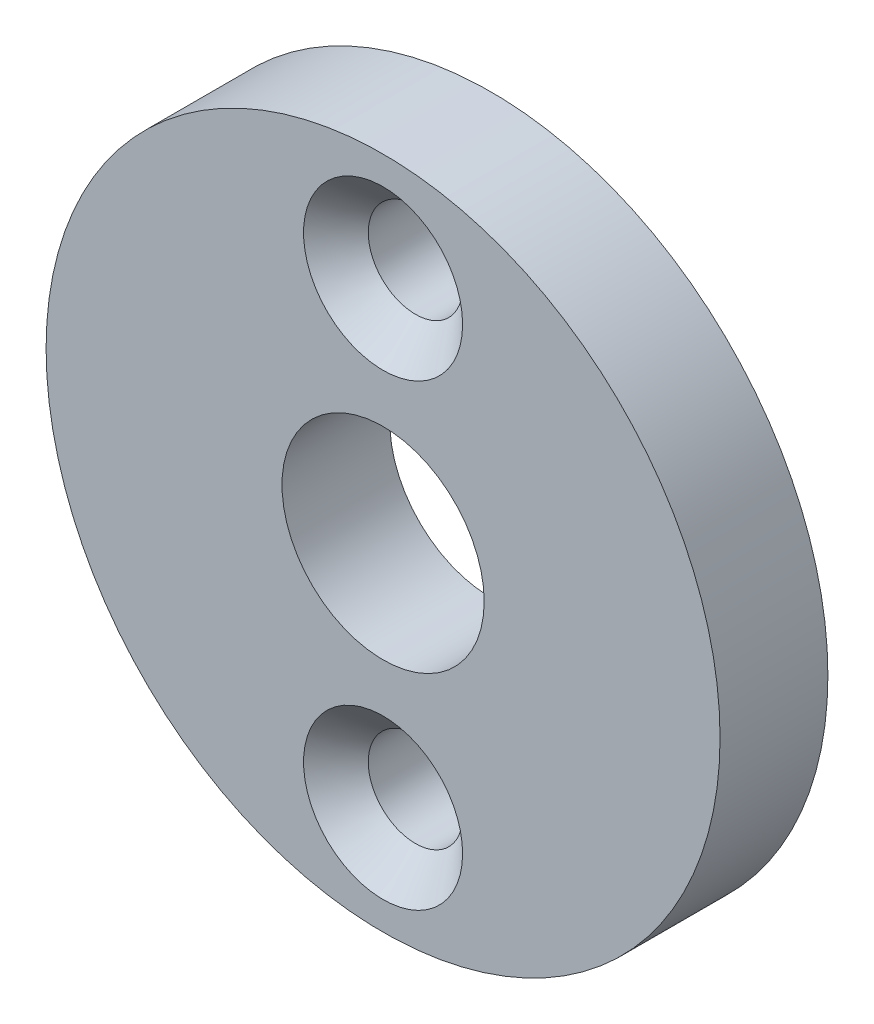
SolidWorks part; units mm, degrees
ref_plane "Front Plane" through (0, 0, 0) normal (0, 0, 1) x (1, 0, 0)
ref_plane "Top Plane" through (0, 0, 0) normal (0, 1, 0) x (1, 0, 0)
ref_plane "Right Plane" through (0, 0, 0) normal (1, 0, 0) x (0, 0, -1)
sketch "Sketch1" plane through (0, 0, 0) normal (0, 0, 1) x (1, 0, 0)
  circle A0 centre (30.875, 8.5) radius 1.75
  circle A1 centre (30.875, 0) radius 12.5
  circle A2 centre (30.875, 0) radius 12.5
  circle A3 centre (30.875, -8.5) radius 1.75
  circle A4 centre (30.875, 0) radius 3.75
  dimension "D2" = 3.5
  dimension "D3" = 7.5
  dimension "D1" = 0
extrude "Boss-Extrude1" add sketch "Sketch1" along normal blind 4
chamfer "Chamfer2" distance 1.2 angle 45 2 edges at (32.625, -8.5, 4) (32.625, 8.5, 4)
